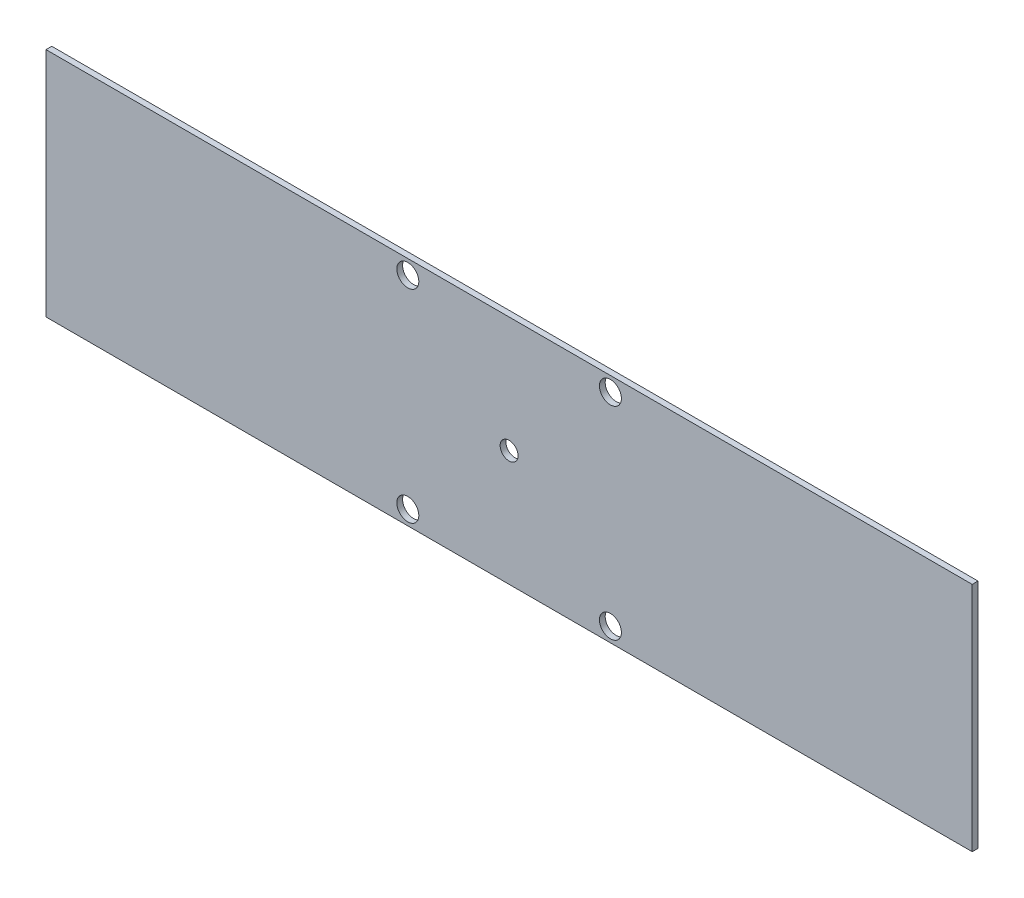
SolidWorks part; units mm, degrees
ref_plane "Front Plane" through (0, 0, 0) normal (0, 0, 1) x (1, 0, 0)
ref_plane "Top Plane" through (0, 0, 0) normal (0, 1, 0) x (1, 0, 0)
ref_plane "Right Plane" through (0, 0, 0) normal (1, 0, 0) x (0, 0, -1)
sketch "Sketch2" plane through (0, 0, 0) normal (0, 0, 1) x (1, 0, 0)
  line L1 (-203.2, -50.8) -> (203.2, -50.8)
  line L2 (-203.2, -50.8) -> (-203.2, 50.8)
  line L3 (-203.2, 50.8) -> (203.2, 50.8)
  line L4 (203.2, -50.8) -> (203.2, 50.8)
  line L5 (-203.2, -50.8) -> (203.2, 50.8) construction
  line L6 (-203.2, 50.8) -> (203.2, -50.8) construction
  point P0 (0, 0)
  dimension "D1" = 406.4
  dimension "D2" = 101.6
extrude "Boss-Extrude2" add sketch "Sketch2" against normal blind 2.54
sketch "Sketch3" plane through (0, 0, 0) normal (0, 0, 1) x (1, 0, 0)
  line L1 (-50.8, -50.8) -> (50.8, -50.8)
  line L2 (-50.8, -50.8) -> (-50.8, 50.8)
  line L3 (-50.8, 50.8) -> (50.8, 50.8)
  line L4 (50.8, -50.8) -> (50.8, 50.8)
  line L5 (-50.8, -50.8) -> (50.8, 50.8) construction
  line L6 (-50.8, 50.8) -> (50.8, -50.8) construction
  circle A0 centre (-44.45, 44.45) radius 4.826
  circle A1 centre (44.45, 44.45) radius 4.826
  circle A2 centre (44.45, -44.45) radius 4.826
  circle A3 centre (-44.45, -44.45) radius 4.826
  point P0 (0, 0)
  point P14 (0, 0)
  dimension "D3" = 9.652
  dimension "D4" = 9.652
  dimension "D5" = 9.652
  dimension "D6" = 9.652
  dimension "D1" = 101.6
  dimension "D2" = 101.6
  dimension "D7" = 6.35
  dimension "D8" = 6.35
  dimension "D9" = 6.35
  dimension "D10" = 6.35
  dimension "D11" = 6.35
extrude "Cut-Extrude1" cut sketch "Sketch3" against normal blind 2.54 contours A3 | A0 | A1 | A2
sketch "Sketch4" plane through (0, 0, 0) normal (0, 0, 1) x (1, 0, 0)
  circle A0 centre (0, 0) radius 3.937
  dimension "D1" = 7.874
extrude "Cut-Extrude2" cut sketch "Sketch4" against normal blind 2.54
sketch "Sketch5" plane through (0, 0, 0) normal (0, 0, 1) x (1, 0, 0)
  line L0 (-203.2, -50.8) -> (203.2, -50.8) construction
  line L1 (-177.8, 38.1) -> (-190.5, 38.1)
  line L2 (-177.8, 38.1) -> (-177.8, -38.1)
  line L3 (-177.8, -38.1) -> (-190.5, -38.1)
  line L4 (-190.5, 38.1) -> (-190.5, -38.1)
  line L5 (-203.2, 50.8) -> (-203.2, -50.8) construction
  dimension "D1" = 76.2
  dimension "D2" = 12.7
  dimension "D3" = 12.7
  dimension "D4" = 12.7
extrude "Boss-Extrude4" add sketch "Sketch5" against normal blind 12.7
mirror "Mirror2" about plane through (0, 0, 0) normal (1, 0, 0) of "Boss-Extrude4"
